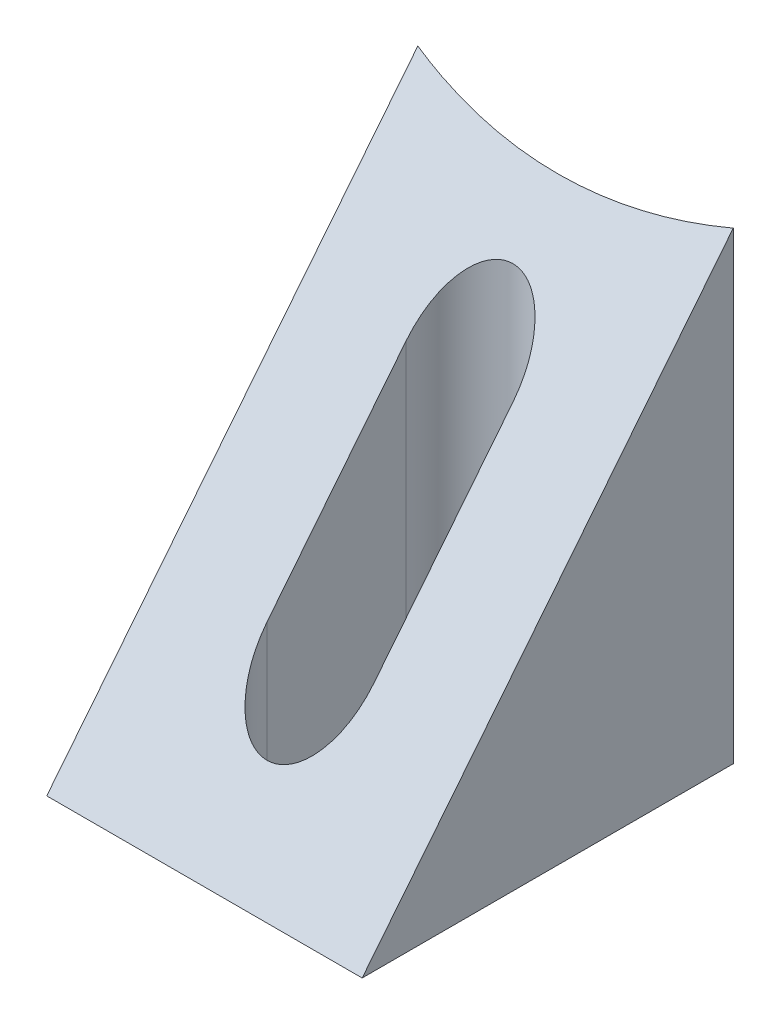
SolidWorks part; units mm, degrees
ref_plane "Front Plane" through (0, 0, 0) normal (0, 0, 1) x (1, 0, 0)
ref_plane "Top Plane" through (0, 0, 0) normal (0, 1, 0) x (1, 0, 0)
ref_plane "Right Plane" through (0, 0, 0) normal (1, 0, 0) x (0, 0, -1)
sketch "Sketch1" plane through (0, 0, 0) normal (0, 1, 0) x (1, 0, 0)
  line L1 (-3.4, 4) -> (3.4, 4)
  line L2 (-3.4, 4) -> (-3.4, -4)
  line L3 (-3.4, -4) -> (3.4, -4)
  line L4 (3.4, 4) -> (3.4, -4)
  line L5 (-3.4, 4) -> (3.4, -4) construction
  line L6 (-3.4, -4) -> (3.4, 4) construction
  point P0 (0, 0)
extrude "Extrude1" add sketch "Sketch1" along normal blind 10
sketch "Sketch2" plane through (3.4, 0, 0) normal (1, 0, 0) x (0, 0, -1)
  line L0 (4, 10) -> (-4, 0)
  line L1 (-4, 0) -> (-4, 10)
  line L2 (-4, 10) -> (4, 10)
extrude "Extrude2" cut sketch "Sketch2" against normal through all
sketch "Sketch3" plane through (0, 0, 0) normal (0, -1, 0) x (1, 0, 0)
  line L0 (0, 4) -> (0, -4) construction
  line L1 (-3.4, 4) -> (3.4, 4) construction
  line L2 (3.4, -4) -> (-3.4, -4) construction
  line L3 (0, 1.5) -> (0, -1.5) construction
  line L4 (1.15, 1.5) -> (1.15, -1.5)
  line L5 (-1.15, 1.5) -> (-1.15, -1.5)
  arc A0 (1.15, 1.5) -> (-1.15, 1.5) centre (0, 1.5) ccw
  arc A1 (-1.15, -1.5) -> (1.15, -1.5) centre (0, -1.5) ccw
  point P8 (0, 0)
extrude "Extrude3" cut sketch "Sketch3" against normal through all
sketch "Sketch4" plane through (0, 0, 0) normal (0, -1, 0) x (1, 0, 0)
  line L0 (-3.4, -4) -> (0, -18.6211) construction
  line L1 (3.4, -4) -> (0, -18.6211) construction
  circle A0 centre (0, -18.6211) radius 15.0112
extrude "Extrude4" cut sketch "Sketch4" against normal through all
